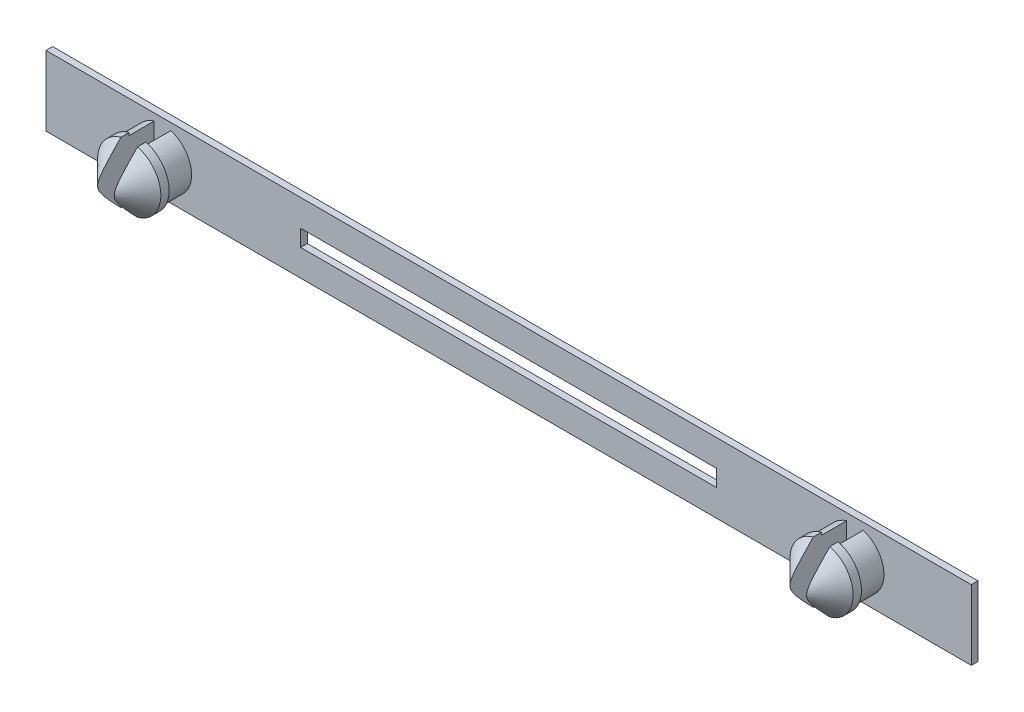
SolidWorks part; units mm, degrees
ref_plane "Přední rovina" through (0, 0, 0) normal (0, 0, 1) x (1, 0, 0)
ref_plane "Horní rovina" through (0, 0, 0) normal (0, 1, 0) x (1, 0, 0)
ref_plane "Pravá rovina" through (0, 0, 0) normal (1, 0, 0) x (0, 0, -1)
sketch "Skica2" plane through (0, 0, 0) normal (0, 0, 1) x (1, 0, 0)
  line L1 (-27.8, 2.1) -> (27.8, 2.1)
  line L2 (-27.8, 2.1) -> (-27.8, -2.1)
  line L3 (-27.8, -2.1) -> (27.8, -2.1)
  line L4 (27.8, 2.1) -> (27.8, -2.1)
  line L5 (-27.8, 2.1) -> (27.8, -2.1) construction
  line L6 (-27.8, -2.1) -> (27.8, 2.1) construction
  line L7 (12.5, 0.5) -> (-12.5, 0.5)
  line L8 (12.5, 0.5) -> (12.5, -0.5)
  line L9 (12.5, -0.5) -> (-12.5, -0.5)
  line L10 (-12.5, 0.5) -> (-12.5, -0.5)
  line L11 (12.5, 0.5) -> (-12.5, -0.5) construction
  line L12 (12.5, -0.5) -> (-12.5, 0.5) construction
  point P0 (0, 0)
  point P5 (0, 0)
  dimension "D1" = 4.2
  dimension "D2" = 55.6
  dimension "D3" = 1
  dimension "D4" = 25
  dimension "D5" = 15.3
  dimension "D6" = 15.3
  dimension "D7" = 0
extrude "Přidat vysunutím2" add sketch "Skica2" along normal blind 0.4
sketch "Skica3" plane through (0, 0, 0.4) normal (0, 0, 1) x (1, 0, 0)
  line L0 (-27.8, 2.1) -> (-27.8, -2.1) construction
  line L1 (27.8, -2.1) -> (27.8, 2.1) construction
  line L2 (27.8, 2.1) -> (-27.8, 2.1) construction
  line L3 (-27.8, -2.1) -> (27.8, -2.1) construction
  circle A0 centre (-20.8, 0) radius 1.75
  circle A1 centre (20.8, 0) radius 1.75
  dimension "D1" = 3.5
  dimension "D3" = 3.5
  dimension "D2" = 7
  dimension "D4" = 7
  dimension "D5" = 2.1
  dimension "D6" = 2.1
extrude "Přidat vysunutím3" add sketch "Skica3" along normal blind 1.5
sketch "Skica5" plane through (0, 0, 1.9) normal (0, 0, 1) x (1, 0, 0)
  circle A0 centre (-20.8, 0) radius 1.9
  circle A1 centre (20.8, 0) radius 1.9
  dimension "D1" = 3.8
  dimension "D2" = 3.8
extrude "Přidat vysunutím5" add sketch "Skica5" along normal blind 2
chamfer "Zkosení2" distance 1.5 angle 45 2 edges at (22.7, 0, 3.9) (-18.9, 0, 3.9)
sketch "Skica7" plane through (0, 0, 3.9) normal (0, 0, 1) x (1, 0, 0)
  line L1 (-20.3, 2.5) -> (-21.3, 2.5)
  line L2 (-20.3, 2.5) -> (-20.3, -2.5)
  line L3 (-20.3, -2.5) -> (-21.3, -2.5)
  line L4 (-21.3, 2.5) -> (-21.3, -2.5)
  line L5 (-20.3, 2.5) -> (-21.3, -2.5) construction
  line L6 (-20.3, -2.5) -> (-21.3, 2.5) construction
  line L7 (20.3, 2.5) -> (21.3, 2.5)
  line L8 (20.3, 2.5) -> (20.3, -2.5)
  line L9 (20.3, -2.5) -> (21.3, -2.5)
  line L10 (21.3, 2.5) -> (21.3, -2.5)
  line L11 (20.3, 2.5) -> (21.3, -2.5) construction
  line L12 (20.3, -2.5) -> (21.3, 2.5) construction
  point P0 (-20.8, 0)
  point P5 (20.8, 0)
  dimension "D1" = 5
  dimension "D2" = 1
  dimension "D3" = 5
  dimension "D4" = 1
extrude "Odebrat vysunutím1" cut sketch "Skica7" against normal blind 3.5
equation "\"1.5.000mm\"=10"
